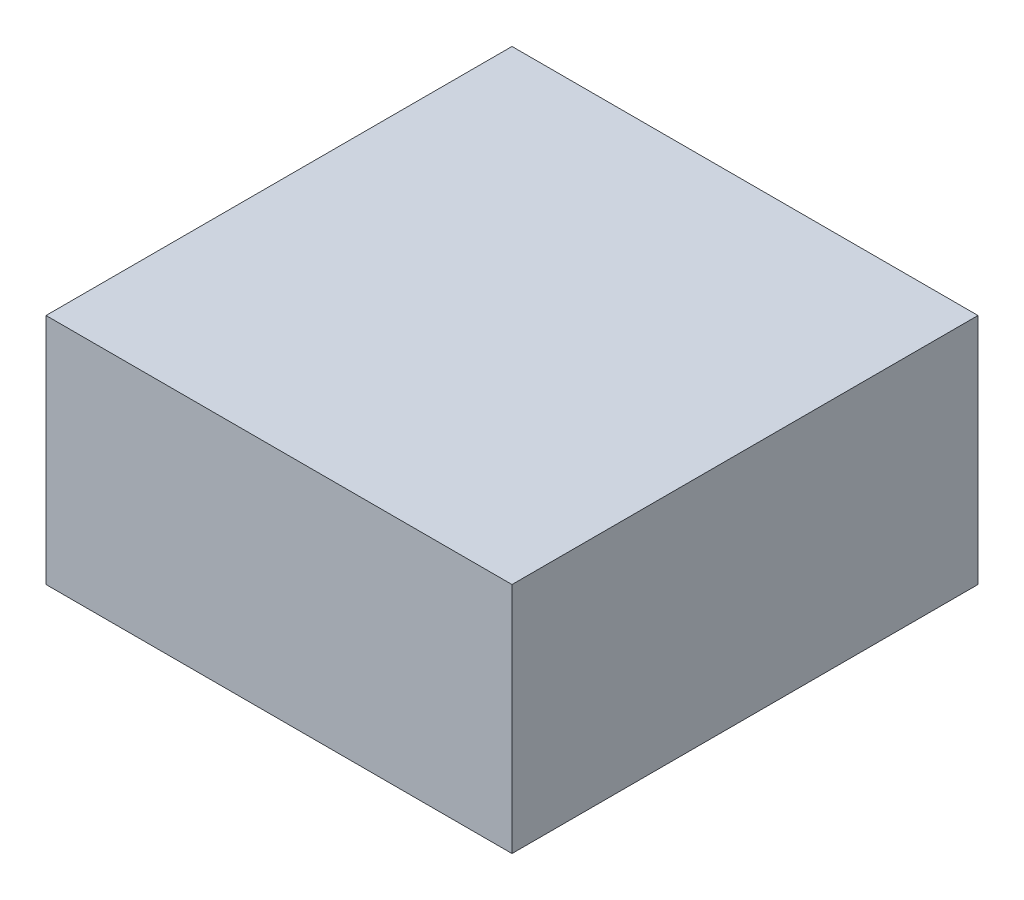
SolidWorks part; units mm, degrees
ref_plane "Front Plane" through (0, 0, 0) normal (0, 0, 1) x (1, 0, 0)
ref_plane "Top Plane" through (0, 0, 0) normal (0, 1, 0) x (1, 0, 0)
ref_plane "Right Plane" through (0, 0, 0) normal (1, 0, 0) x (0, 0, -1)
sketch "Sketch1" plane through (0, 0, 0) normal (0, 0, 1) x (1, 0, 0)
  line L1 (-10, -5) -> (10, -5)
  line L2 (-10, -5) -> (-10, 5)
  line L3 (-10, 5) -> (10, 5)
  line L4 (10, -5) -> (10, 5)
  line L5 (0, 5) -> (0, -5) construction
  line L6 (-10, 0) -> (10, 0) construction
  point P0 (0, 0)
  dimension "D1" = 20
  dimension "D2" = 10
extrude "Boss-Extrude1" add sketch "Sketch1" along normal blind 20
sketch "Sketch2" plane through (0, 0, 20) normal (0, 0, 1) x (1, 0, 0)
  line L0 (-10, -5) -> (10, -5) construction
  line L1 (0, 0) -> (0, -5) construction
  line L3 (10, 5) -> (-10, 5) construction
  circle A0 centre (-7.5, 4) radius 0.5
  circle A1 centre (7.5, 4) radius 0.5
  dimension "D1" = 1
  dimension "D2" = 7.5
  dimension "D3" = 1
ref_plane "Plane1" through (7.5, 0, 0) normal (1, 0, 0) x (0, 0, -1)
sketch "Sketch3" plane through (7.5, 0, 0) normal (1, 0, 0) x (0, 0, -1)
  line L3 (-20, 4) -> (-5, 4)
  line L4 (-20, 4.5) -> (-20, 3.5) construction
  line L5 (-20, 5) -> (0, 5) construction
  arc A0 (-5, 4) -> (-4, 5) centre (-5, 5) ccw
  dimension "D1" = 1
  dimension "D2" = 15
sweep "ag/agcl electrodes" add profiles "Sketch2" path "Sketch3"
sketch "Sketch4" plane through (0, -5, 0) normal (0, 1, 0) x (1, 0, 0)
  line L0 (0, -11.4373) -> (0, -13.4201) construction
  line L1 (-2.0803, -12.5) -> (1.6023, -12.5) construction
  spline S0 degree 3 poles (-2.0861, -12.5392) (-1.3776, -12.1296) (-0.8241, -11.549) (0.2513, -11.3226) (1.3726, -11.7466) (2.6529, -13.5718) (0.7805, -13.1045) (-0.1221, -13.5063) (-0.9948, -13.461) (-1.5864, -13.1169) (-2.0861, -12.5392) (-1.3776, -12.1296) (-0.8241, -11.549) knots -0.204834 -0.133435 -0.089031 0 0.049563 0.182818 0.303261 0.461561 0.613381 0.684438 0.795166 0.866565 0.910969 1 1.049563 1.182818 1.303261 only from (-1.3298, -12.0471) to (-1.3298, -12.0471)
extrude "slice" add sketch "Sketch4" along normal blind 0.3 separate body
